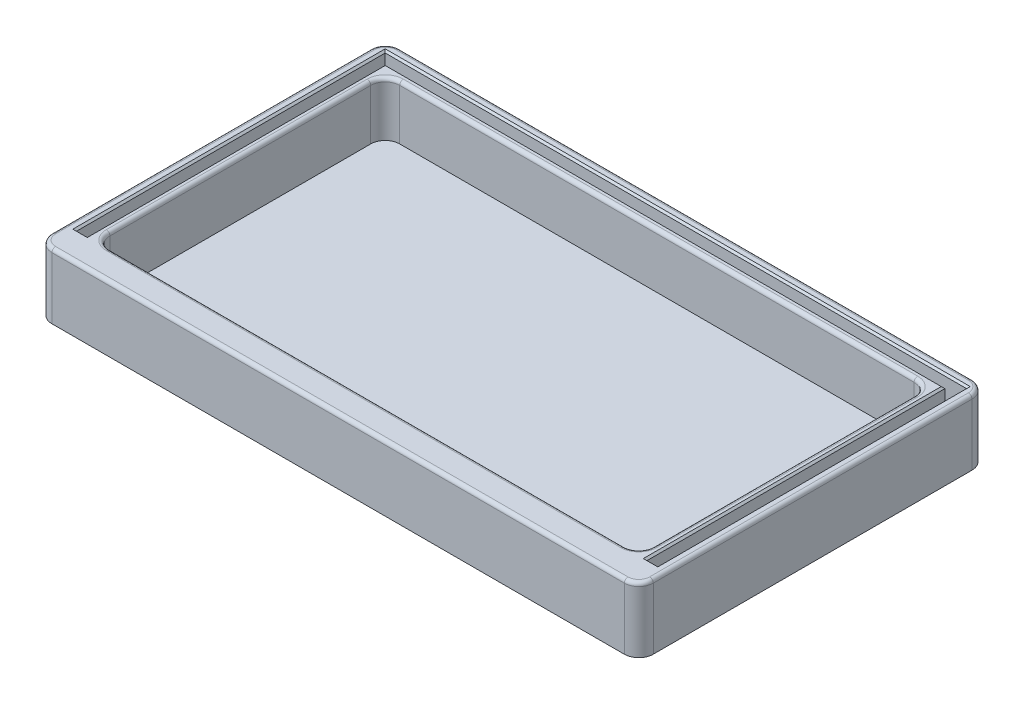
SolidWorks part; units mm, degrees
ref_plane "Front Plane" through (0, 0, 0) normal (0, 0, 1) x (1, 0, 0)
ref_plane "Top Plane" through (0, 0, 0) normal (0, 1, 0) x (1, 0, 0)
ref_plane "Right Plane" through (0, 0, 0) normal (1, 0, 0) x (0, 0, -1)
sketch "Sketch1" plane through (0, 0, 0) normal (0, 1, 0) x (1, 0, 0)
  line L1 (-64.9244, 29.2933) -> (101.0756, 29.2933)
  line L2 (-64.9244, 29.2933) -> (-64.9244, -66.7067)
  line L3 (-64.9244, -66.7067) -> (101.0756, -66.7067)
  line L4 (101.0756, 29.2933) -> (101.0756, -66.7067)
  dimension "D1" = 166
  dimension "D2" = 96
extrude "Boss-Extrude1" add sketch "Sketch1" along normal blind 18
sketch "Sketch2" plane through (0, 18, 0) normal (0, 1, 0) x (1, 0, 0)
  line L0 (101.0756, 29.2933) -> (-64.9244, 29.2933) construction
  line L1 (-56.9244, 21.2933) -> (93.0756, 21.2933)
  line L2 (-56.9244, 21.2933) -> (-56.9244, -58.7067)
  line L3 (-56.9244, -58.7067) -> (93.0756, -58.7067)
  line L4 (93.0756, 21.2933) -> (93.0756, -58.7067)
  line L5 (-64.9244, 29.2933) -> (-64.9244, -66.7067) construction
  dimension "D1" = 150
  dimension "D2" = 80
  dimension "D3" = 8
  dimension "D4" = 8
extrude "Cut-Extrude1" cut sketch "Sketch2" against normal blind 15
sketch "Sketch9" plane through (0, 18, 0) normal (0, 1, 0) x (1, 0, 0)
  line L0 (101.0756, 29.2933) -> (-64.9244, 29.2933) construction
  line L1 (-62.1744, 26.5433) -> (98.3256, 26.5433)
  line L2 (-62.1744, 26.5433) -> (-62.1744, -58.7067)
  line L3 (-62.1744, -58.7067) -> (-59.1744, -58.7067)
  line L4 (98.3256, 26.5433) -> (98.3256, -58.7067)
  line L5 (-59.1744, 23.5433) -> (95.3256, 23.5433)
  line L6 (-59.1744, 23.5433) -> (-59.1744, -58.7067)
  line L8 (95.3256, 23.5433) -> (95.3256, -58.7067)
  line L9 (-64.9244, 29.2933) -> (-64.9244, -66.7067) construction
  line L10 (101.0756, -66.7067) -> (101.0756, 29.2933) construction
  line L11 (-64.9244, -66.7067) -> (101.0756, -66.7067) construction
  line L12 (95.3256, -58.7067) -> (98.3256, -58.7067)
  point P16 (0, 0)
  point P17 (0, 0)
  dimension "D1" = 3
  dimension "D2" = 3
  dimension "D4" = 3
  dimension "D5" = 2.75
  dimension "D6" = 2.75
  dimension "D7" = 2.75
  dimension "D8" = 8
extrude "Cut-Extrude5" cut sketch "Sketch9" against normal blind 10
fillet "Fillet1" radius 4 4 edges at (-64.9244, 9, -29.2933) (101.0756, 9, -29.2933) (101.0756, 9, 66.7067) (-64.9244, 9, 66.7067)
fillet "Fillet2" radius 4 4 edges at (93.0756, 10.5, 58.7067) (93.0756, 10.5, -21.2933) (-56.9244, 10.5, -21.2933) (-56.9244, 10.5, 58.7067)
fillet "Fillet5" radius 1 16 edges at (-55.7529, 18, 57.5351) (-56.9244, 18, 18.7067) (18.0756, 18, 58.7067) (91.904, 18, 57.5351) (93.0756, 18, 18.7067) (91.904, 18, -20.1217) (18.0756, 18, -21.2933) (-55.7529, 18, -20.1217) (-63.7529, 18, -28.1217) (18.0756, 18, -29.2933) (99.904, 18, -28.1217) (101.0756, 18, 18.7067) (99.904, 18, 65.5351) (18.0756, 18, 66.7067) (-64.9244, 18, 18.7067) (-63.7529, 18, 65.5351)
chamfer "Chamfer1" distance 0.5 angle 45 8 edges at (95.3256, 18, 17.5817) (96.8256, 18, 58.7067) (98.3256, 18, 16.0817) (18.0756, 18, -23.5433) (-59.1744, 18, 17.5817) (-60.6744, 18, 58.7067) (-62.1744, 18, 16.0817) (18.0756, 18, -26.5433)
equation "\"Inner width\"= 80"
equation "\"Inner length\" = 150"
equation "\"pannel thick\" = 2.5"
equation "\"base thickness\" = 3"
equation "\"D1@Sketch1\" = \"Inner length\" + \"Side thickness\" * 2"
equation "\"D2@Sketch1\" = \"Inner width\" + \"Side thickness\" * 2"
equation "\"Base inner height\"= 15"
equation "\"D1@Boss-Extrude1\"=\"Base inner height\"+\"base thickness\""
equation "\"D1@Sketch2\"=\"Inner length\""
equation "\"D2@Sketch2\"=\"Inner width\""
equation "\"D3@Sketch2\"=\"Side thickness\""
equation "\"D4@Sketch2\" = \"Side thickness\""
equation "\"D1@Cut-Extrude1\"=\"Base inner height\""
equation "\"Side thickness\" = 8"
equation "\"pannel seat depth\"= 10"
equation "\"D1@Cut-Extrude5\"=\"pannel seat depth\""
equation "\"D8@Sketch9\"=\"Side thickness\""
equation "\"D6@Sketch9\"=(\"Side thickness\"-\"pannel thick\")/2"
equation "\"D7@Sketch9\"=(\"Side thickness\"-\"pannel thick\")/2"
equation "\"D5@Sketch9\"=(\"Side thickness\"-\"pannel thick\")/2"
